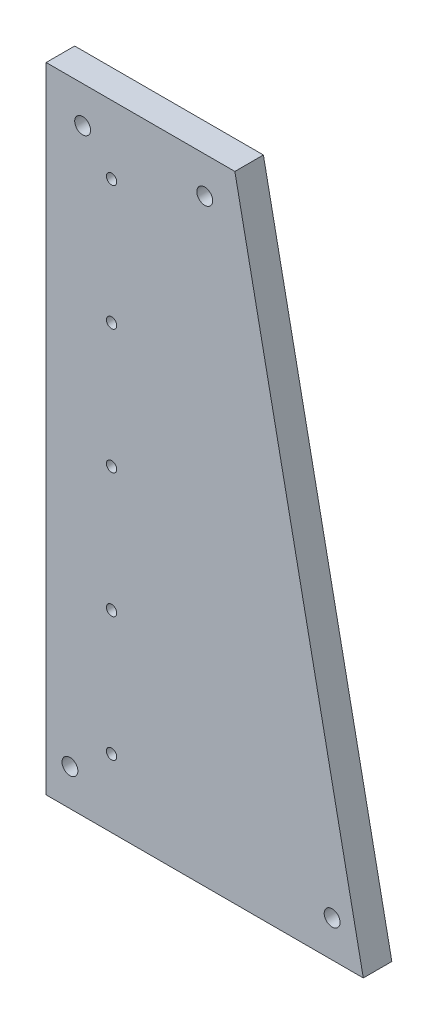
SolidWorks part; units mm, degrees
ref_plane "Front Plane" through (0, 0, 0) normal (0, 0, 1) x (1, 0, 0)
ref_plane "Top Plane" through (0, 0, 0) normal (0, 1, 0) x (1, 0, 0)
ref_plane "Right Plane" through (0, 0, 0) normal (1, 0, 0) x (0, 0, -1)
sketch "Sketch1" plane through (0, 0, 0) normal (0, 0, 1) x (1, 0, 0)
  line L0 (-65.3107, 157.0796) -> (15.6893, -242.9204)
  line L1 (-184.3107, 157.0796) -> (-65.3107, 157.0796)
  line L2 (-184.3107, 157.0796) -> (-184.3107, -242.9204)
  line L3 (-184.3107, -242.9204) -> (-65.3107, -242.9204)
  line L4 (-65.3107, 157.0796) -> (-65.3107, -242.9204) construction
  line L5 (15.6893, -242.9204) -> (-65.3107, -242.9204)
  dimension "D1" = 400
  dimension "D2" = 119
  dimension "D3" = 200
extrude "Boss-Extrude1" add sketch "Sketch1" along normal blind 18
sketch "Sketch2" plane through (0, 0, 0) normal (0, 0, -1) x (-1, 0, 0)
  line L0 (60.6532, 134.0796) -> (184.3107, 134.0796) construction
  line L1 (-15.6893, -242.9204) -> (65.3107, 157.0796) construction
  line L2 (184.3107, 157.0796) -> (184.3107, -242.9204) construction
  line L3 (65.3107, 157.0796) -> (184.3107, 157.0796) construction
  line L4 (143.0607, 157.0796) -> (143.0607, -242.9204) construction
  line L5 (184.3107, -242.9204) -> (-15.6893, -242.9204) construction
  line L6 (-11.0318, -219.9204) -> (184.3107, -219.9204) construction
  circle A0 centre (84.3107, 134.0796) radius 5
  circle A1 centre (161.3107, 134.0796) radius 5
  circle A2 centre (143.0607, 114.0796) radius 3.25
  circle A3 centre (143.0607, 35.5796) radius 3.25
  circle A4 centre (143.0607, -42.9204) radius 3.25
  circle A5 centre (143.0607, -121.4204) radius 3.25
  circle A6 centre (143.0607, -199.9204) radius 3.25
  circle A7 centre (169.3107, -219.9204) radius 5
  circle A8 centre (3.9682, -219.9204) radius 5
  dimension "D2" = 10
  dimension "D6" = 43
  dimension "D7" = 6.5
  dimension "D10" = 15
  dimension "D11" = 15
  dimension "D1" = 23
  dimension "D3" = 100
  dimension "D4" = 23
  dimension "D5" = 41.25
  dimension "D9" = 23
  dimension "D8" = 5
extrude "Cut-Extrude1" cut sketch "Sketch2" against normal through all
